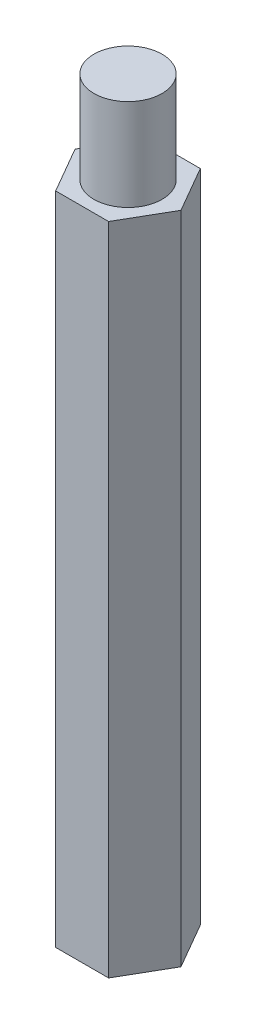
SolidWorks part; units mm, degrees
material "黄铜"
ref_plane "前视基准面" through (0, 0, 0) normal (0, 0, 1) x (1, 0, 0)
ref_plane "上视基准面" through (0, 0, 0) normal (0, 1, 0) x (1, 0, 0)
ref_plane "右视基准面" through (0, 0, 0) normal (1, 0, 0) x (0, 0, -1)
sketch "草图1" plane through (0, 0, 0) normal (0, 1, 0) x (1, 0, 0)
  line L1 (4.0415, 0) -> (2.0207, 3.5)
  line L2 (2.0207, 3.5) -> (-2.0207, 3.5)
  line L3 (-2.0207, 3.5) -> (-4.0415, 0)
  line L4 (-4.0415, 0) -> (-2.0207, -3.5)
  line L5 (-2.0207, -3.5) -> (2.0207, -3.5)
  line L6 (2.0207, -3.5) -> (4.0415, 0)
  circle A0 centre (0, 0) radius 3.5 construction
  dimension "D1" = 7
extrude "凸台-拉伸1" add sketch "草图1" along normal blind 50
sketch "草图2" plane through (0, 50, 0) normal (0, 1, 0) x (1, 0, 0)
  circle A0 centre (0, 0) radius 2.6
  dimension "D1" = 5.2
extrude "切除-拉伸1" cut sketch "草图2" against normal through all
ref_plane "基准面1" through (0, 10, 0) normal (0, -1, 0) x (-1, 0, 0)
sketch "草图3" plane through (0, 10, 0) normal (0, -1, 0) x (-1, 0, 0)
  circle A0 centre (0, 0) radius 2.6 construction
  circle A1 centre (0, 0) radius 2.6
extrude "凸台-拉伸2" add sketch "草图3" against normal offset from surface (47 mm away) 7 up to face at (0, 50, 2.6) offset beyond the face yes
